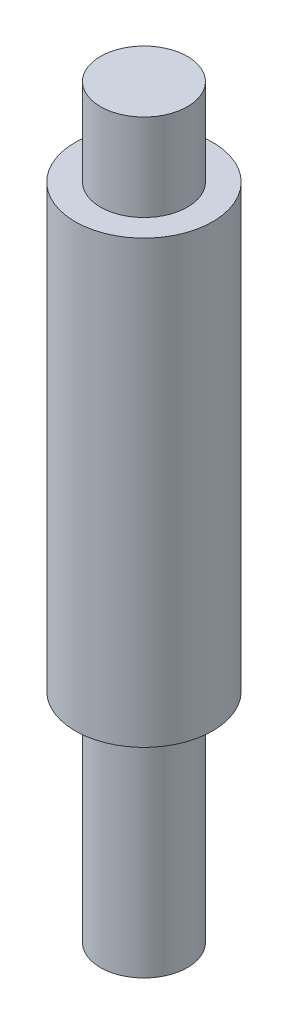
SolidWorks part; units mm, degrees
ref_plane "Front Plane" through (0, 0, 0) normal (0, 0, 1) x (1, 0, 0)
ref_plane "Top Plane" through (0, 0, 0) normal (0, 1, 0) x (1, 0, 0)
ref_plane "Right Plane" through (0, 0, 0) normal (1, 0, 0) x (0, 0, -1)
sketch "Sketch1" plane through (0, 0, 0) normal (0, 1, 0) x (1, 0, 0)
  circle A0 centre (0, 0) radius 6.35
  dimension "D1" = 12.7
extrude "BushingSprocketSpace" add sketch "Sketch1" along normal blind 31.75
sketch "Sketch2" plane through (0, 31.75, 0) normal (0, 1, 0) x (1, 0, 0)
  circle A0 centre (0, 0) radius 10.033
  dimension "D1" = 20.066
extrude "Boss-Extrude2" add sketch "Sketch2" along normal blind 64.3509
sketch "Sketch3" plane through (0, 96.1009, 0) normal (0, 1, 0) x (1, 0, 0)
  circle A0 centre (0, 0) radius 6.35
  dimension "D1" = 12.7
extrude "Boss-Extrude3" add sketch "Sketch3" along normal blind 12.7
hole_wizard "#10-24 Tapped Hole2" positions "3DSketch10" profile "Sketch11" tap size "#10-24" standard "ANSI Inch"
sketch3d "3DSketch10"
  line L0 (0, 0, 0) -> (0, 108.8009, 0) construction
  line L1 (0, 108.8009, 0) -> (0, 96.1009, 0) construction
  point P0 (0, 64.2518, -10.033)
  dimension "D1" = 31.8491
sketch "Sketch11" plane through (0, 64.2518, -10.033) normal (1, 0, 0) x (0, 1, 0)
  line L0 (0, 0) -> (0, 11.3008)
  line L1 (0, 11.3008) -> (1.8986, 10.16)
  line L2 (1.8986, 10.16) -> (1.8986, 0.635)
  line L3 (1.8986, 0.635) -> (2.5337, 0)
  line L5 (2.5337, 0) -> (0, 0)
  line L6 (-1.8986, 0.635) -> (-2.5337, 0) construction
  line L10 (0, 11.3008) -> (-1.8987, 10.16) construction
  line L11 (0, -6.35) -> (0, 107.95) construction
  dimension "Tap Drill Dia." = 3.7973
  dimension "Tap Drill Depth" = 10.16
  dimension "Near C'Sink Dia." = 5.0673
  dimension "Near C'Sink Angle" = 90
  dimension "Drill Angle" = 118
